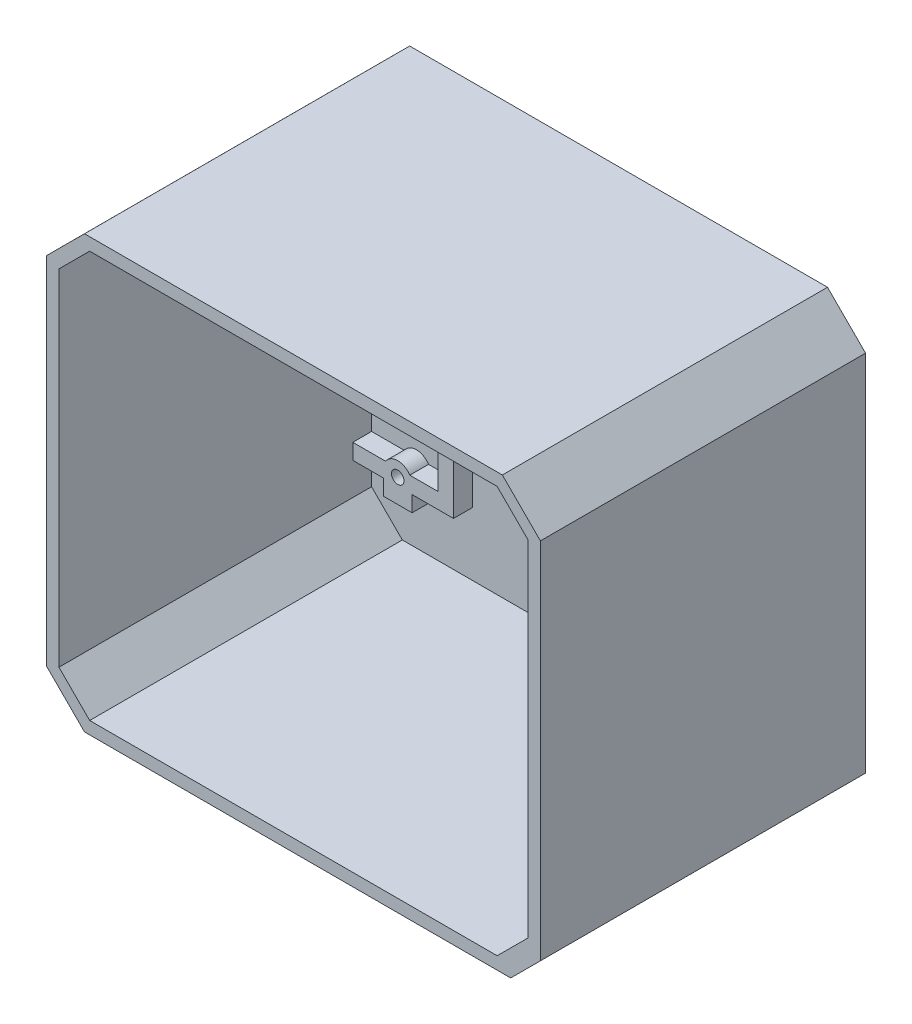
SolidWorks part; units mm, degrees
ref_plane "Front Plane" through (0, 0, 0) normal (0, 0, 1) x (1, 0, 0)
ref_plane "Top Plane" through (0, 0, 0) normal (0, 1, 0) x (1, 0, 0)
ref_plane "Right Plane" through (0, 0, 0) normal (1, 0, 0) x (0, 0, -1)
sketch "Sketch2" plane through (0, 0, 0) normal (0, 0, 1) x (1, 0, 0)
  line L0 (7.0704, 67) -> (62.0787, 67)
  line L1 (5.0821, 0) -> (64.0909, 0)
  line L2 (0.1535, 4.9273) -> (0.1535, 64.0678)
  line L3 (5.0821, 69) -> (64.0909, 69)
  line L4 (69.1535, 5.0681) -> (69.1535, 63.9268)
  line L6 (2.1535, 62.0879) -> (2.1535, 6.9169)
  line L7 (7.0704, 2) -> (62.0787, 2)
  line L8 (67.1535, 61.9216) -> (67.1535, 7.0833)
  line L9 (9.2454, 44.45) -> (9.2454, 43.1985) construction
  line L10 (3.0535, 49.55) -> (15.6035, 49.55)
  line L11 (3.0535, 49.55) -> (3.0535, 44.45)
  line L12 (0, 70.9946) -> (4.9989, 70.9946) construction
  line L13 (3.0535, 44.45) -> (7.3157, 44.45)
  line L14 (15.6035, 49.55) -> (15.6035, 44.45)
  line L15 (18.1456, 44.4709) -> (18.1456, 12.0709)
  line L16 (0.1535, 64.0678) -> (5.0821, 69)
  line L17 (2.1535, 62.0879) -> (7.0704, 67)
  line L19 (10.2504, 13.3209) -> (10.5004, 13.3209)
  line L20 (0.1535, 4.9273) -> (5.0821, 0)
  line L21 (2.1535, 6.9169) -> (7.0704, 2)
  line L22 (15.6456, 44.4709) -> (18.1456, 44.4709)
  line L23 (15.7505, 41.9485) -> (15.7505, 14.5709)
  line L26 (2.1535, 14.5709) -> (7.486, 14.5709)
  line L28 (69.1535, 5.0681) -> (64.0909, 0)
  line L29 (67.1535, 7.0833) -> (62.0787, 2)
  line L30 (64.0909, 69) -> (69.1535, 63.9268)
  line L31 (62.0787, 67) -> (67.1535, 61.9216)
  line L32 (2.0704, 12.0709) -> (7.486, 12.0709)
  line L34 (2.1535, 44.4485) -> (7.3147, 44.4485)
  line L36 (2.0704, 41.9485) -> (7.3147, 41.9485)
  line L38 (8.0835, 11.4734) -> (8.0835, 8.6259)
  line L39 (8.0835, 8.6259) -> (10.5835, 8.6259)
  line L40 (10.5835, 11.4734) -> (10.5835, 8.6259)
  line L41 (11.1811, 14.5709) -> (15.7505, 14.5709)
  line L42 (11.1811, 12.0709) -> (18.1456, 12.0709)
  line L43 (11.1751, 44.45) -> (15.6035, 44.45)
  line L44 (11.1761, 44.4485) -> (17.3391, 44.4485)
  line L45 (11.1761, 41.9485) -> (15.7505, 41.9485)
  circle A0 centre (9.2454, 43.1985) radius 2.3
  arc A1 (12.5614, 29.3869) -> (6.1286, 29.3724) centre (9.3335, 34.4637) ccw
  arc A2 (6.385, 28.7755) -> (12.2823, 28.7732) centre (9.3335, 28.4476) ccw
  arc A3 (12.5614, 29.3869) -> (12.2823, 28.7732) centre (15.2238, 27.8058) ccw
  arc A4 (6.1286, 29.3724) -> (6.385, 28.7755) centre (3.4671, 27.8755) cw
  circle A5 centre (9.2454, 43.1985) radius 1
  circle A6 centre (9.3335, 13.3209) radius 2.2307
  circle A7 centre (9.3335, 13.3209) radius 0.9169
  dimension "D9" = 7.18
  dimension "D11" = 53.6791
  dimension "D12" = 7.18
  dimension "D13" = 6.417
  dimension "D1" = 12.55
  dimension "D2" = 5.1
  dimension "D3" = 2
  dimension "D4" = 2
  dimension "D5" = 2
  dimension "D6" = 0.9
  dimension "D7" = 17.45
  dimension "D8" = 1.2515
  dimension "D10" = 32.5363
  dimension "D14" = 2.5
  dimension "D15" = 2.5
  dimension "D16" = 1.25
  dimension "D18" = 1.25
  dimension "D19" = 1.25
extrude "Boss-Extrude3" add sketch "Sketch2" along normal blind 2
sketch "Sketch7" plane through (0, 0, 2) normal (0, 0, 1) x (1, 0, 0)
  line L0 (2.1535, 62.0879) -> (2.1535, 6.9169) construction
  line L1 (7.0704, 67) -> (62.0787, 67) construction
  line L2 (11.2642, 14.57) -> (18.2535, 14.57)
  line L3 (15.7535, 44.45) -> (18.2535, 44.45)
  line L4 (15.7535, 44.45) -> (15.7535, 44.4485)
  line L6 (18.2535, 44.45) -> (18.2535, 16.5346)
  line L7 (2.1535, 44.4485) -> (7.3147, 44.4485)
  line L8 (2.1535, 44.4485) -> (2.1535, 41.9485)
  line L9 (2.1535, 41.9485) -> (7.3147, 41.9485)
  line L11 (2.1535, 14.57) -> (7.4028, 14.57)
  line L12 (2.1535, 14.57) -> (2.1535, 12.07)
  line L13 (2.1535, 12.07) -> (7.4028, 12.07)
  line L14 (18.2535, 14.57) -> (18.2535, 12.07)
  line L16 (15.7535, 16.5346) -> (15.7535, 12.07)
  line L17 (15.7535, 12.07) -> (18.2535, 12.07)
  line L18 (18.2535, 16.5346) -> (18.2535, 12.07)
  line L20 (7.0335, 12.07) -> (7.0335, 9.5478)
  line L21 (7.0335, 9.5478) -> (11.6335, 9.5478)
  line L22 (11.6335, 12.07) -> (11.6335, 9.5478)
  line L23 (11.2642, 12.07) -> (18.2535, 12.07)
  line L24 (15.7535, 41.9485) -> (15.7535, 16.5346)
  line L25 (11.1761, 44.4485) -> (17.3319, 44.4485)
  line L26 (11.1761, 41.9485) -> (15.7535, 41.9485)
  arc A0 (7.3157, 44.45) -> (7.3147, 44.4485) centre (9.2454, 43.1985) ccw
  arc A1 (11.1751, 44.45) -> (7.3157, 44.45) centre (9.2454, 43.1985) ccw construction
  circle A2 centre (9.2454, 43.1985) radius 1
  arc A3 (11.2642, 14.57) -> (7.4028, 14.57) centre (9.3335, 13.32) ccw
  circle A4 centre (9.3335, 13.32) radius 1
  arc A5 (3.3174, 34.4637) -> (9.3199, 40.4798) centre (9.3335, 34.4637) ccw
  arc A6 (12.5614, 29.3869) -> (6.1286, 29.3724) centre (9.3335, 34.4637) ccw construction
  arc A7 (7.3147, 41.9485) -> (11.1761, 41.9485) centre (9.2454, 43.1985) ccw
  arc A8 (11.1761, 44.4485) -> (9.2454, 45.4985) centre (9.2454, 43.1985) ccw
  arc A9 (7.4028, 12.07) -> (11.2642, 12.07) centre (9.3335, 13.32) ccw
  dimension "D1" = 7.18
  dimension "D3" = 6.42
  dimension "D2" = 53.68
  dimension "D4" = 2.5
  dimension "D6" = 1.25
  dimension "D7" = 2.5
  dimension "D8" = 1.25
extrude "Boss-Extrude5" add sketch "Sketch7" along normal blind 3
ref_plane "Plane1" through (34.6535, 0, 0) normal (-1, 0, 0) x (0, 0, 1)
sketch "Sketch15" plane through (0, 0, 2) normal (0, 0, 1) x (1, 0, 0)
  circle A0 centre (9.3335, 34.4637) radius 6.0161
  circle A1 centre (9.3335, 28.4476) radius 2.9667
mirror "Mirror4" about plane through (34.6535, 0, 0) normal (-1, 0, 0) of "Boss-Extrude3", "Boss-Extrude5"
extrude "Cut-Extrude5" cut sketch "Sketch15" against normal blind 3 contours A1 | A0
sketch "Sketch21" plane through (0, 0, 2) normal (0, 0, 1) x (1, 0, 0)
  line L0 (3.3174, 34.4637) -> (3.3174, 54.9397) construction
  line L1 (15.3496, 34.4637) -> (15.3496, 54.9397) construction
  line L2 (3.3174, 44.7017) -> (7.5046, 44.7017)
  line L3 (10.9861, 44.7017) -> (15.3496, 44.7017)
  line L4 (15.3496, 44.7017) -> (15.3496, 49.7017)
  line L5 (15.3496, 49.7017) -> (3.3174, 49.7017)
  line L6 (3.3174, 49.7017) -> (3.3174, 44.7017)
  arc A0 (12.2086, 29.1791) -> (6.4584, 29.1791) centre (9.3335, 34.4637) ccw construction
  arc A1 (11.1761, 44.4485) -> (7.3147, 44.4485) centre (9.2454, 43.1985) ccw construction
  arc A2 (7.5046, 44.7017) -> (10.9861, 44.7017) centre (9.2454, 43.1985) cw
  dimension "D1" = 5
extrude "Cut-Extrude6" cut sketch "Sketch21" against normal blind 3 contours L2 A2 L3 L4 L5 L6
mirror "Mirror5" about plane through (34.6535, 0, 0) normal (-1, 0, 0) of "Cut-Extrude5"
sketch "Sketch29" plane through (0, 0, 2) normal (0, 0, 1) x (1, 0, 0)
  line L0 (3.3174, 34.4637) -> (3.3174, 55.1273) construction
  line L1 (15.3496, 34.4637) -> (15.3496, 55.1273) construction
  line L2 (3.3174, 44.7955) -> (7.5902, 44.7955)
  line L3 (10.9005, 44.7955) -> (15.3496, 44.7955)
  line L4 (15.3496, 44.7955) -> (15.3496, 49.7955)
  line L5 (15.3496, 49.7955) -> (3.3174, 49.7955)
  line L6 (3.3174, 49.7955) -> (3.3174, 44.7955)
  arc A0 (12.2086, 29.1791) -> (6.4584, 29.1791) centre (9.3335, 34.4637) ccw construction
  arc A1 (11.1761, 44.4485) -> (10.9861, 44.7017) centre (9.2454, 43.1985) ccw construction
  arc A2 (11.1761, 44.4485) -> (7.3147, 44.4485) centre (9.2454, 43.1985) ccw construction
  arc A3 (10.9005, 44.7955) -> (7.5902, 44.7955) centre (9.2454, 43.1985) ccw
  dimension "D1" = 5
extrude "Cut-Extrude7" cut sketch "Sketch29" against normal blind 10
mirror "Mirror9" about plane through (34.6535, 0, 0) normal (-1, 0, 0) of "Cut-Extrude7"
other "SurfaceCut1"
sketch "Sketch31" plane through (34.6535, 0, 0) normal (1, 0, 0) x (0, 0, -1)
  line L1 (-2, 67) -> (0, 67)
  line L2 (-2, 67) -> (-2, 2)
  line L3 (-2, 2) -> (0, 2)
  line L4 (0, 67) -> (0, 2)
extrude "Boss-Extrude8" add sketch "Sketch31" along normal blind 5 contours L2 L1 L4 L3
ref_plane "Plane4" through (39.6535, 0, 0) normal (1, 0, 0) x (0, 0, -1)
mirror "Mirror13" about plane through (39.6535, 0, 0) normal (1, 0, 0) of "Boss-Extrude3", "Boss-Extrude5"
sketch "Sketch36" plane through (0, 0, 2) normal (0, 0, 1) x (1, 0, 0)
  circle A0 centre (9.3335, 34.4637) radius 6.0124
extrude "Cut-Extrude11" cut sketch "Sketch36" against normal blind 5
sketch "Sketch37" plane through (0, 0, 2) normal (0, 0, 1) x (1, 0, 0)
  circle A0 centre (9.3335, 28.4476) radius 2.9667
extrude "Cut-Extrude12" cut sketch "Sketch37" against normal blind 5
sketch "Sketch38" plane through (0, 0, 2) normal (0, 0, 1) x (1, 0, 0)
  line L0 (15.3458, 34.4945) -> (15.3458, 50.1443) construction
  line L2 (12.1535, 49.7955) -> (15.3458, 49.7955)
  line L3 (12.1535, 49.7955) -> (12.1535, 44.7127)
  line L4 (12.1535, 44.7127) -> (15.3458, 44.7127)
  line L5 (15.3458, 49.7955) -> (15.3458, 44.7127)
  arc A0 (12.2077, 29.1828) -> (12.1535, 39.7738) centre (9.3335, 34.4637) ccw construction
extrude "Cut-Extrude13" cut sketch "Sketch38" against normal blind 5
sketch "Sketch40" plane through (0, 0, 2) normal (0, 0, 1) x (1, 0, 0)
  line L0 (79.1535, 4.7505) -> (79.1535, 62.9169)
  line L2 (74.4031, 0) -> (6.242, 0)
  line L3 (77.1535, 62.0879) -> (77.1535, 44.4485) construction
  line L4 (6.2425, 69) -> (73.0645, 69)
  line L5 (7.0704, 67) -> (72.2366, 67) construction
  line L6 (7.0704, 2) -> (72.2366, 2) construction
  line L7 (0.1535, 6.0884) -> (0.1535, 62.9169)
  line L8 (2.1535, 62.0879) -> (2.1535, 44.4485) construction
  line L9 (0.1535, 62.9169) -> (6.2425, 69)
  line L10 (2.1535, 62.0879) -> (7.0704, 67) construction
  line L11 (73.0645, 69) -> (79.1535, 62.9169)
  line L12 (77.1535, 62.0879) -> (72.2366, 67) construction
  line L13 (0.1535, 6.0884) -> (6.242, 0)
  line L14 (2.1535, 6.9169) -> (7.0704, 2) construction
  line L15 (74.4031, 0) -> (79.1535, 4.7505)
  line L16 (7.0704, 67) -> (72.2366, 67)
  line L17 (72.2366, 67) -> (77.1535, 62.0879)
  line L18 (77.1535, 62.0879) -> (77.1535, 6.9169)
  line L19 (77.1535, 6.9169) -> (72.2366, 2)
  line L20 (72.2366, 2) -> (7.0704, 2)
  line L21 (7.0704, 2) -> (2.1535, 6.9169)
  line L22 (2.1535, 6.9169) -> (2.1535, 62.0879)
  line L23 (2.1535, 62.0879) -> (7.0704, 67)
  point P17 (4.6119, 64.5439)
  dimension "D1" = 2
  dimension "D2" = 2
  dimension "D3" = 2
  dimension "D4" = 2
  dimension "D5" = 2
  dimension "D6" = 2
  dimension "D7" = 2
extrude "Boss-Extrude13" add sketch "Sketch40" along normal blind 50 and the other way blind 2
